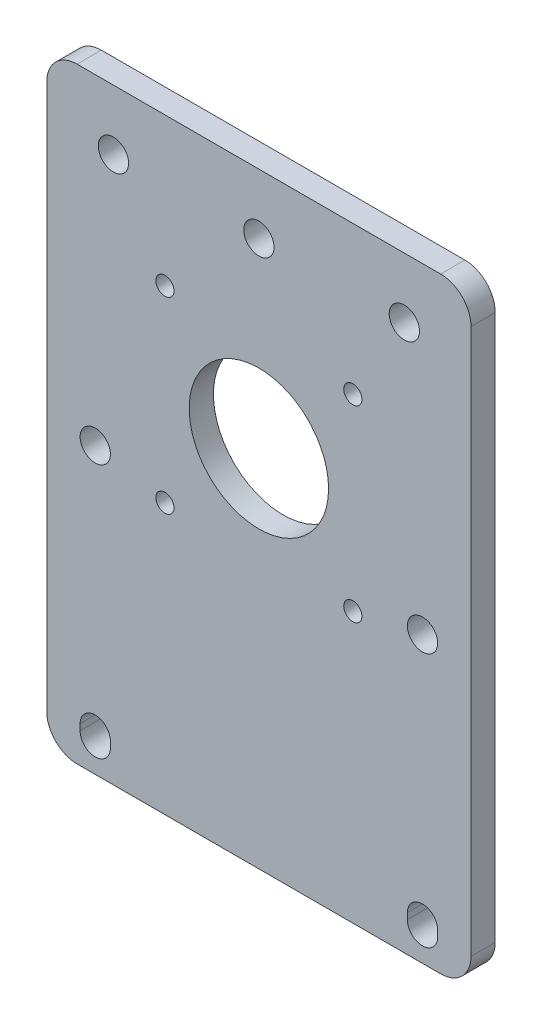
SolidWorks part; units mm, degrees
ref_plane "Front" through (0, 0, 0) normal (0, 0, 1) x (1, 0, 0)
ref_plane "Top" through (0, 0, 0) normal (0, 1, 0) x (1, 0, 0)
ref_plane "Right" through (0, 0, 0) normal (1, 0, 0) x (0, 0, -1)
sketch "Sketch4" plane through (0, 0, 0) normal (0, 0, 1) x (1, 0, 0)
  line L0 (-27, -44) -> (-27, -45) construction
  line L1 (-35, 50) -> (35, 50)
  line L2 (-35, 50) -> (-35, -50)
  line L3 (-35, -50) -> (35, -50)
  line L4 (35, 50) -> (35, -50)
  line L5 (-35, 50) -> (35, -50) construction
  line L6 (-35, -50) -> (35, 50) construction
  line L7 (-24.5, -44) -> (-24.5, -45)
  line L8 (-29.5, -44) -> (-29.5, -45)
  line L9 (0, -47.1607) -> (0, 39.6245) construction
  line L10 (27, -44) -> (27, -45) construction
  line L11 (24.5, -44) -> (24.5, -45)
  line L12 (29.5, -44) -> (29.5, -45)
  circle A0 centre (-27, -3) radius 2.5
  arc A1 (-24.5, -44) -> (-29.5, -44) centre (-27, -44) ccw
  arc A2 (-29.5, -45) -> (-24.5, -45) centre (-27, -45) ccw
  arc A3 (24.5, -44) -> (29.5, -44) centre (27, -44) cw
  arc A4 (29.5, -45) -> (24.5, -45) centre (27, -45) cw
  circle A5 centre (27, -3) radius 2.5
  point P0 (0, 0)
  point P10 (-27, -44.5)
  point P19 (27, -44.5)
  dimension "D3" = 27
  dimension "D6" = 2.5
  dimension "D8" = 5
  dimension "D1" = 70
  dimension "D2" = 100
  dimension "D4" = 41
  dimension "D5" = 1
  dimension "D7" = 5
extrude "Boss-Extrude2" add sketch "Sketch4" along normal blind 4
sketch "Sketch5" plane through (0, 0, 4) normal (0, 0, 1) x (1, 0, 0)
  line L0 (0, 46.583) -> (0, -17.262) construction
  line L1 (-44.8343, 10.0767) -> (52.8956, 10.0767) construction
  circle A0 centre (0, 10.0767) radius 11.5
  circle A1 centre (27, -3) radius 2.5 construction
  circle A2 centre (-15.5, 25.5767) radius 1.5
  circle A9 centre (15.5, 25.5767) radius 1.5
  circle A10 centre (15.5, -5.4233) radius 1.5
  circle A11 centre (-15.5, -5.4233) radius 1.5
  dimension "D1" = 23
  dimension "D3" = 3
  dimension "D2" = 30
  dimension "D4" = 15.5
  dimension "D5" = 15.5
extrude "Cut-Extrude2" cut sketch "Sketch5" against normal through all
sketch "Sketch6" plane through (0, 0, 4) normal (0, 0, 1) x (1, 0, 0)
  line L0 (0, 37.2831) -> (0, 4.0651) construction
  line L1 (-10, 50.0767) -> (10, 50.0767) construction
  line L2 (-10, 50.0767) -> (-10, 30.0767) construction
  line L3 (-10, 30.0767) -> (10, 30.0767) construction
  line L4 (10, 50.0767) -> (10, 30.0767) construction
  line L5 (-10, 50.0767) -> (10, 30.0767) construction
  line L6 (-10, 30.0767) -> (10, 50.0767) construction
  circle A0 centre (0, 10.0767) radius 11.5 construction
  circle A1 centre (24, 40.0767) radius 2.5
  circle A2 centre (-24, 40.0767) radius 2.5
  circle A3 centre (0, 40.0767) radius 2.5
  point P0 (0, 40.0767)
  dimension "D4" = 5
  dimension "D6" = 5
  dimension "D1" = 20
  dimension "D2" = 20
  dimension "D3" = 30
  dimension "D5" = 24
extrude "Cut-Extrude3" cut sketch "Sketch6" against normal through all
fillet "Fillet1" radius 5 4 edges at (-35, -50, 2) (35, -50, 2) (35, 50, 2) (-35, 50, 2)
